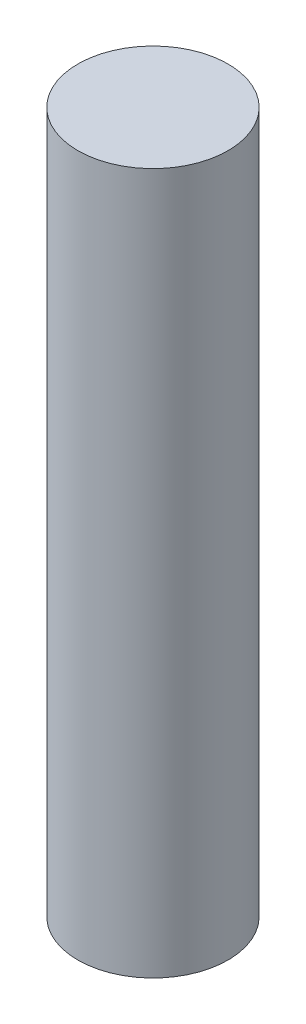
SolidWorks part; units mm, degrees
ref_plane "前视基准面" through (0, 0, 0) normal (0, 0, 1) x (1, 0, 0)
ref_plane "上视基准面" through (0, 0, 0) normal (0, 1, 0) x (1, 0, 0)
ref_plane "右视基准面" through (0, 0, 0) normal (1, 0, 0) x (0, 0, -1)
sketch "草图1" plane through (0, 0, 0) normal (0, 1, 0) x (1, 0, 0)
  circle A0 centre (0, 0) radius 7.5
  dimension "D1" = 15
extrude "凸台-拉伸1" add sketch "草图1" along normal blind 70
